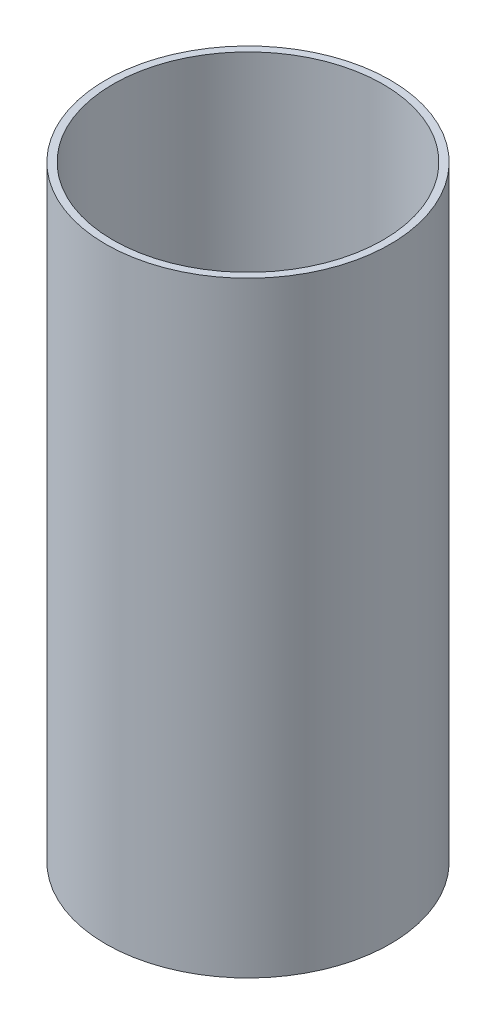
SolidWorks part; units mm, degrees
material "PVC Rigid"
ref_plane "Front Plane" through (0, 0, 0) normal (0, 0, 1) x (1, 0, 0)
ref_plane "Top Plane" through (0, 0, 0) normal (0, 1, 0) x (1, 0, 0)
ref_plane "Right Plane" through (0, 0, 0) normal (1, 0, 0) x (0, 0, -1)
sketch "Sketch1" plane through (0, 0, 0) normal (0, 1, 0) x (1, 0, 0)
  circle A0 centre (0, 0) radius 93.6625
  circle A1 centre (0, 0) radius 88.9
  dimension "D1" = 187.325
  dimension "D2" = 177.8
extrude "Boss-Extrude1" add sketch "Sketch1" along normal mid plane 399.034
